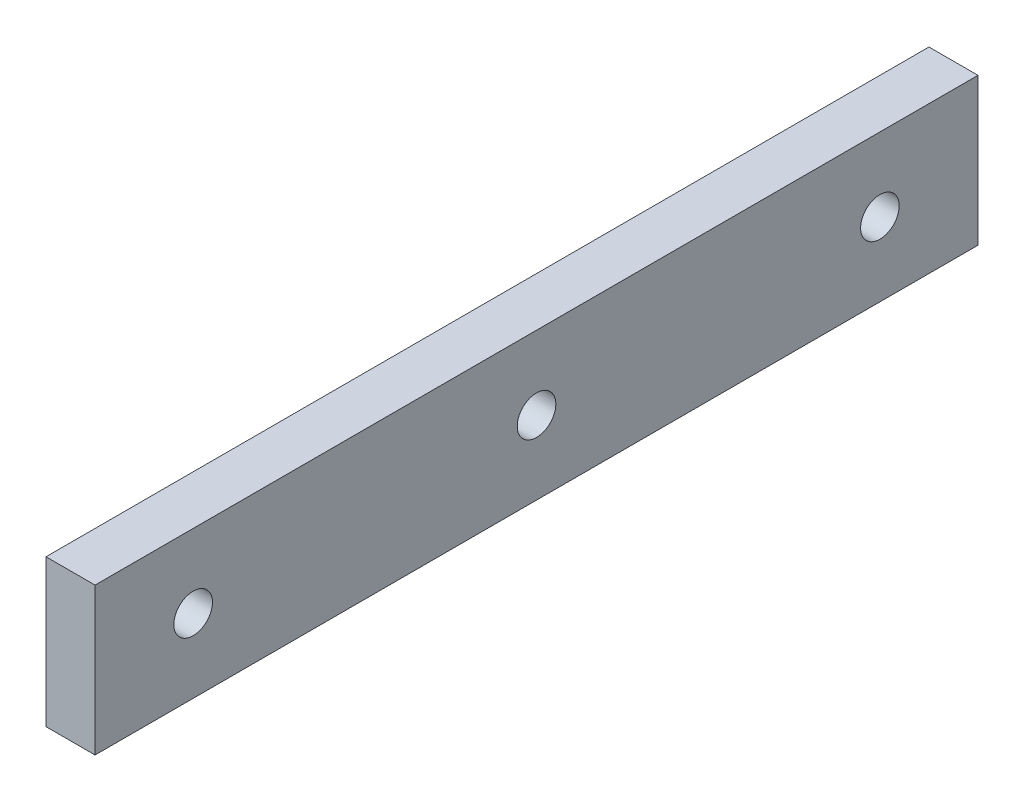
SolidWorks part; units mm, degrees
material "SS 304 (Default)"
ref_plane "Front Plane" through (0, 0, 0) normal (0, 0, 1) x (1, 0, 0)
ref_plane "Top Plane" through (0, 0, 0) normal (0, 1, 0) x (1, 0, 0)
ref_plane "Right Plane" through (0, 0, 0) normal (1, 0, 0) x (0, 0, -1)
sketch "Sketch1" plane through (0, 0, 0) normal (0, 0, 1) x (1, 0, 0)
  line L1 (-3.175, 9.525) -> (3.175, 9.525)
  line L2 (-3.175, 9.525) -> (-3.175, -9.525)
  line L3 (-3.175, -9.525) -> (3.175, -9.525)
  line L4 (3.175, 9.525) -> (3.175, -9.525)
  line L5 (-3.175, 9.525) -> (3.175, -9.525) construction
  line L6 (-3.175, -9.525) -> (3.175, 9.525) construction
  point P0 (0, 0)
  dimension "Width" = 6.35
  dimension "Height" = 19.05
extrude "Extrude1" add sketch "Sketch1" along normal mid plane 114.3
hole_wizard "M6x1.0 Tapped Hole1" positions "Sketch3" profile "Sketch2" tap size "M6x1.0" standard "Ansi Metric" end condition up to next
sketch "Sketch3" plane through (3.175, 0, 0) normal (1, 0, 0) x (0, 0, -1)
  line L0 (-44.45, 0) -> (44.45, 0) construction
  line L1 (57.15, -9.525) -> (57.15, 9.525) construction
  point P0 (-44.45, 0)
  point P1 (44.45, 0)
  dimension "D2" = 12.7
sketch "Sketch2" plane through (3.175, 0, 44.45) normal (0, 1, 0) x (0, 0, -1)
  line L0 (0, 0) -> (0, 6.35)
  line L1 (0, 6.35) -> (2.5, 6.35)
  line L2 (2.5, 6.35) -> (2.5, 0)
  line L5 (2.5, 0) -> (0, 0)
  line L11 (0, -6.35) -> (0, 107.95) construction
  dimension "Thru Tap Drill Dia." = 5
  dimension "Thru Tap Drill Depth" = 6.35
cosmetic thread "Hole Thread1" parameters "D2"=6
cosmetic thread "Hole Thread2" parameters "D2"=6
hole_wizard "M6x1.0 Tapped Hole2" positions "Sketch8" profile "Sketch7" tap size "M6x1.0" standard "ANSI Metric" end condition through all
sketch "Sketch8" plane through (3.175, 0, 0) normal (1, 0, 0) x (0, 0, -1)
  line L0 (-57.15, 0) -> (57.15, 0) construction
  line L1 (-57.15, -9.525) -> (-57.15, 9.525) construction
  line L2 (57.15, -9.525) -> (57.15, 9.525) construction
  point P0 (0, 0)
sketch "Sketch7" plane through (3.175, 0, 0) normal (0, 1, 0) x (0, 0, -1)
  line L0 (0, 0) -> (0, 6.35)
  line L1 (0, 6.35) -> (2.5, 6.35)
  line L2 (2.5, 6.35) -> (2.5, 0)
  line L5 (2.5, 0) -> (0, 0)
  line L11 (0, -6.35) -> (0, 107.95) construction
  dimension "Thru Tap Drill Dia." = 5
  dimension "Thru Tap Drill Depth" = 6.35
cosmetic thread "Hole Thread3" parameters "D2"=6
